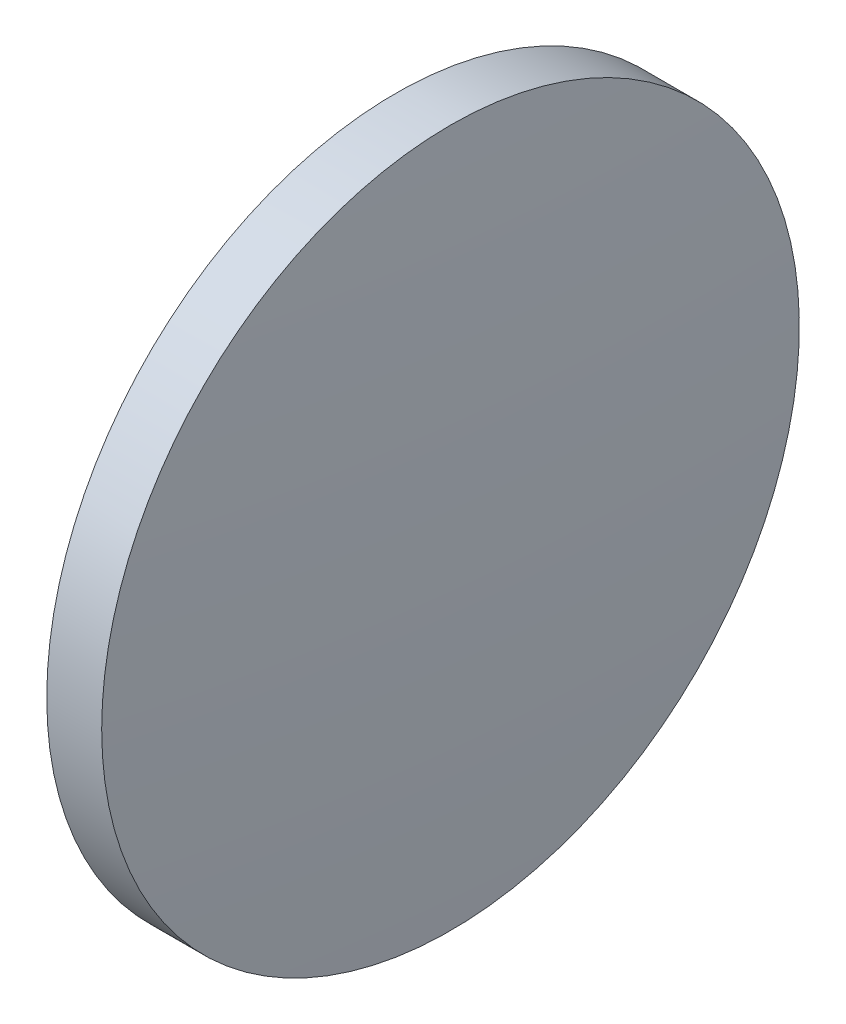
SolidWorks part; units mm, degrees
ref_plane "前视基准面" through (0, 0, 0) normal (0, 0, 1) x (1, 0, 0)
ref_plane "上视基准面" through (0, 0, 0) normal (0, 1, 0) x (1, 0, 0)
ref_plane "右视基准面" through (0, 0, 0) normal (1, 0, 0) x (0, 0, -1)
sketch "草图1" plane through (0, 0, 0) normal (0, 0, 1) x (1, 0, 0)
  line L0 (471.5839, 184.5774) -> (490.3799, 184.5774) construction
  line L1 (477.3221, 184.5774) -> (477.3221, 197.2774)
  line L2 (477.3221, 197.2774) -> (479.3221, 197.2774)
  line L3 (479.7221, 184.5774) -> (477.3221, 184.5774)
  arc A0 (479.7221, 184.5774) -> (479.3221, 197.2774) centre (277.9096, 184.5774) ccw
revolve "旋转1" add sketch "草图1" angle 360 about L0
